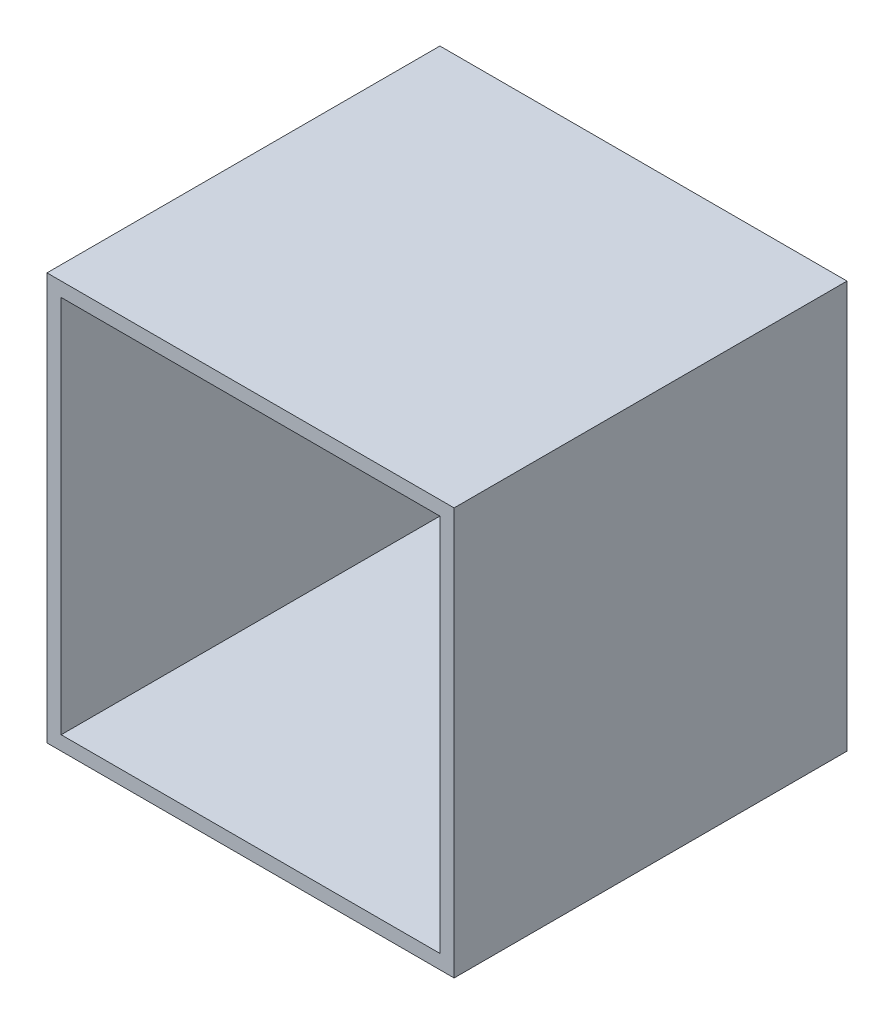
SolidWorks part; units mm, degrees
ref_plane "Front Plane" through (0, 0, 0) normal (0, 0, 1) x (1, 0, 0)
ref_plane "Top Plane" through (0, 0, 0) normal (0, 1, 0) x (1, 0, 0)
ref_plane "Right Plane" through (0, 0, 0) normal (1, 0, 0) x (0, 0, -1)
sketch "Sketch1" plane through (0, 0, 0) normal (0, 0, 1) x (1, 0, 0)
  line L0 (43, 43) -> (-43, 43)
  line L1 (40, 40) -> (-40, 40)
  line L2 (40, 40) -> (40, -40)
  line L3 (40, -40) -> (-40, -40)
  line L4 (-40, 40) -> (-40, -40)
  line L5 (40, 40) -> (-40, -40) construction
  line L6 (40, -40) -> (-40, 40) construction
  line L7 (-43, 43) -> (-43, -43)
  line L8 (43, -43) -> (-43, -43)
  line L9 (43, 43) -> (43, -43)
  point P0 (0, 0)
  dimension "D1" = 80
  dimension "D2" = 80
  dimension "D3" = 3
extrude "Boss-Extrude1" add sketch "Sketch1" along normal blind 80
sketch "Sketch2" plane through (0, 0, 0) normal (0, 0, -1) x (-1, 0, 0)
  line L1 (-43, 43) -> (43, 43)
  line L2 (-43, 43) -> (-43, -43)
  line L3 (-43, -43) -> (43, -43)
  line L4 (43, 43) -> (43, -43)
extrude "Boss-Extrude2" add sketch "Sketch2" along normal blind 3
